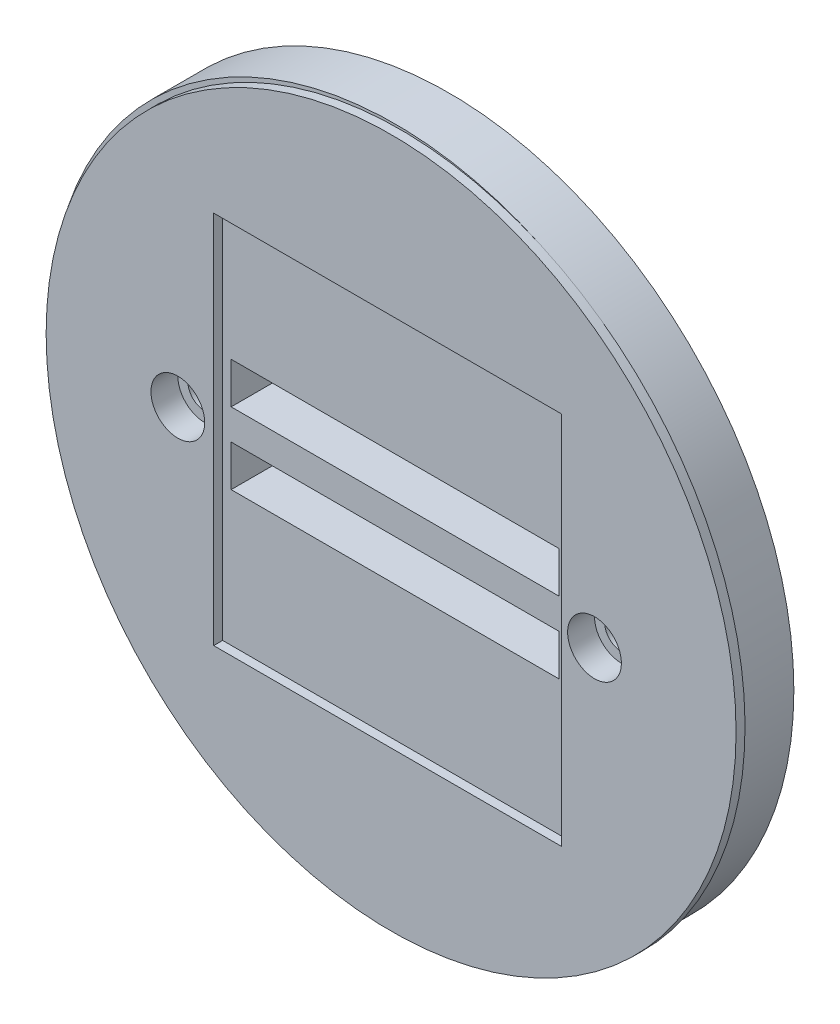
SolidWorks part; units mm, degrees
material "ABS"
ref_plane "Front Plane" through (0, 0, 0) normal (0, 0, 1) x (1, 0, 0)
ref_plane "Top Plane" through (0, 0, 0) normal (0, 1, 0) x (1, 0, 0)
ref_plane "Right Plane" through (0, 0, 0) normal (1, 0, 0) x (0, 0, -1)
sketch "Sketch1" plane through (0, 0, 0) normal (0, 0, 1) x (1, 0, 0)
  line L0 (18.3, 6.6) -> (18.3, 2)
  line L2 (-18.3, 6.6) -> (18.3, 6.6)
  line L3 (18.3, -1.4) -> (-18.3, -1.4)
  line L4 (-18.3, 2) -> (-18.3, 6.6)
  line L5 (-18.3, -1.4) -> (-18.3, -6)
  line L6 (-18.3, -6) -> (18.3, -6)
  line L7 (18.3, -6) -> (18.3, -1.4)
  line L8 (18.3, 2) -> (-18.3, 2)
  circle A0 centre (-23.25, 0) radius 1.875
  circle A1 centre (0, 0) radius 34.7 construction
  circle A2 centre (23.25, 0) radius 1.875
  circle A6 centre (0, 0) radius 38.5
  dimension "D2" = 69.4
  dimension "D3" = 18.3
  dimension "D6" = 18.3
  dimension "D7" = 23.25
  dimension "D4" = 23.25
  dimension "D5" = 77
  dimension "D9" = 4.6
  dimension "D10" = 3.75
  dimension "D8" = 3.75
extrude "Main Flange Coupling" add sketch "Sketch1" against normal blind 6
sketch "Sketch2" plane through (0, 0, 0) normal (0, 0, 1) x (1, 0, 0)
  line L0 (-19.25, 20.75) -> (19.55, 20.75)
  line L1 (-19.25, 20.75) -> (-19.25, -21.05)
  line L2 (-19.25, -21.05) -> (19.55, -21.05)
  line L3 (19.55, 20.75) -> (19.55, -21.05)
  line L4 (-19.25, 20.75) -> (19.55, -21.05) construction
  line L5 (-19.25, -21.05) -> (19.55, 20.75) construction
  circle A0 centre (0.55, -0.25) radius 38.5
  circle A1 centre (-23.25, 0) radius 1.65
  circle A2 centre (23.25, 0) radius 1.65
  dimension "D3" = 77
  dimension "D4" = 3.3
  dimension "D5" = 3.3
  dimension "D1" = 38.8
  dimension "D2" = 41.8
  dimension "D6" = 21
  dimension "D7" = 19
extrude "Boss-Extrude1" add sketch "Sketch2" along normal blind 1
sketch "Sketch3" plane through (0, 0, 1) normal (0, 0, 1) x (1, 0, 0)
  circle A0 centre (-23.25, 0) radius 3
  circle A1 centre (23.25, 0) radius 3
  dimension "D1" = 6
  dimension "D2" = 6
extrude "Cut-Extrude1" cut sketch "Sketch3" against normal blind 3
equation "\"D4@Sketch2\"= 3 + \"tol1@parametersSketch@prostheticParameters.SLDPRT\""
equation "\"D5@Sketch2\"= 3 + \"tol1@parametersSketch@prostheticParameters.SLDPRT\""
equation "\"D1@Sketch2\"= 38.5 + \"tol2@parametersSketch@prostheticParameters.SLDPRT\""
equation "\"D2@Sketch2\"= 41.5 + \"tol2@parametersSketch@prostheticParameters.SLDPRT\""
equation "\"D8@Sketch1\"= 3.45 + \"tol1@parametersSketch@prostheticParameters.SLDPRT\""
equation "\"D10@Sketch1\"= 3.45 + \"tol1@parametersSketch@prostheticParameters.SLDPRT\""
equation "\"D3@Sketch1\"= 18 + \"tol2@parametersSketch@prostheticParameters.SLDPRT\""
equation "\"D6@Sketch1\" = 18 + \"tol2@parametersSketch@prostheticParameters.SLDPRT\""
equation "\"D9@Sketch1\"= 4 + \"tol2@parametersSketch@prostheticParameters.SLDPRT\" * 2"
